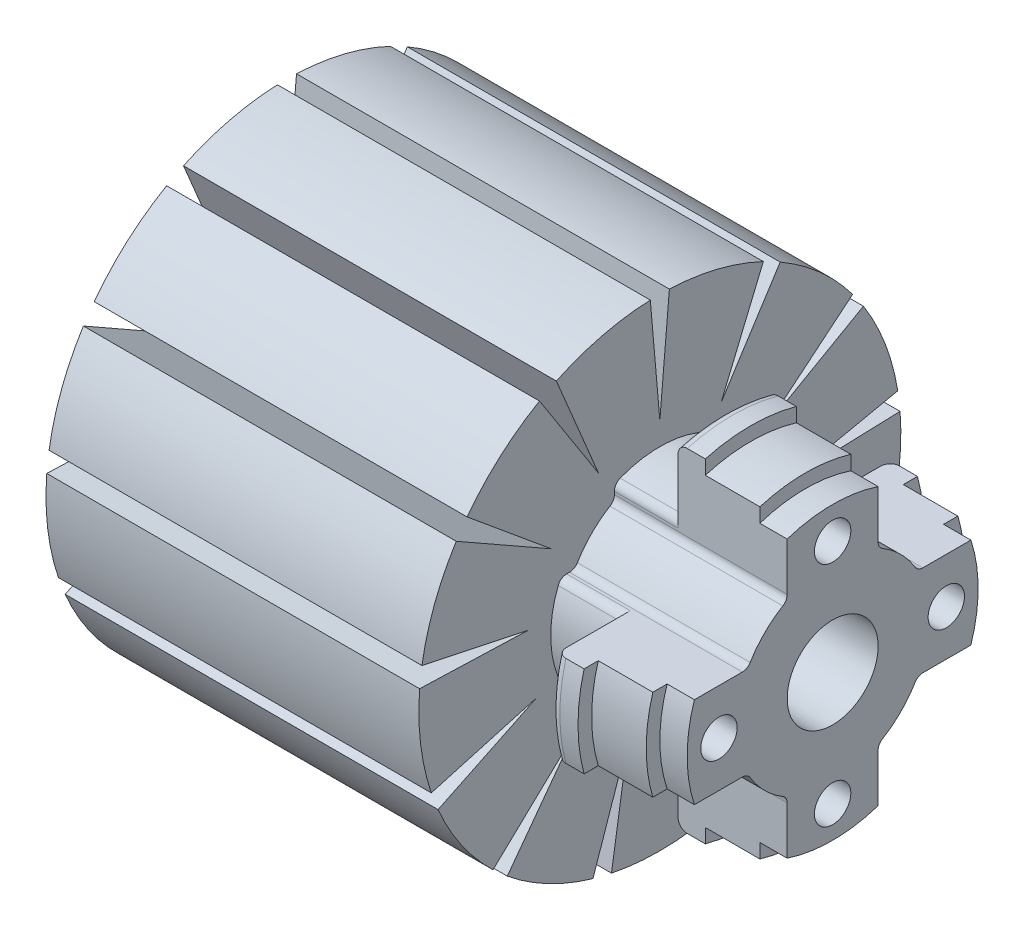
SolidWorks part; units mm, degrees
ref_plane "Front Plane" through (0, 0, 0) normal (0, 0, 1) x (1, 0, 0)
ref_plane "Top Plane" through (0, 0, 0) normal (0, 1, 0) x (1, 0, 0)
ref_plane "Right Plane" through (0, 0, 0) normal (1, 0, 0) x (0, 0, -1)
sketch "Sketch1" plane through (0, 0, 0) normal (1, 0, 0) x (0, 0, -1)
  circle A0 centre (0, 0) radius 26.5
  circle A1 centre (0, 0) radius 5
  dimension "D1" = 53
  dimension "D2" = 10
extrude "Extrude1" add sketch "Sketch1" along normal blind 60
sketch "Sketch2" plane through (0, 0, 0) normal (0, 0, 1) x (1, 0, 0)
  line L0 (0, 0) -> (31, 0) construction
  line L1 (0, 26.5) -> (0, -26.5) construction
  line L3 (60, 26.5) -> (41, 26.5)
  line L4 (60, 26.5) -> (60, 0)
  line L6 (41, 26.5) -> (41, 12)
  line L8 (60, 0) -> (60, 16)
  line L9 (60, 16) -> (57, 16)
  line L12 (57, 16) -> (57, 17.5)
  line L13 (57, 17.5) -> (51, 17.5)
  line L16 (51, 17.5) -> (51, 19)
  line L17 (51, 19) -> (48, 19)
  line L18 (48, 12) -> (48, 19)
  line L21 (48, 12) -> (41, 12)
  dimension "D1" = 12
  dimension "D2" = 7.5
  dimension "D3" = 9
  dimension "D4" = 10.5
  dimension "D5" = 7
  dimension "D6" = 3
  dimension "D7" = 6
  dimension "D8" = 19
revolve "Cut-Revolve1" cut sketch "Sketch2" angle 360 about L0
sketch "Sketch3" plane through (60, 0, 0) normal (1, 0, 0) x (0, 0, -1)
  circle A0 centre (0, 12.5) radius 2
  circle A1 centre (12.5, 0) radius 2
  circle A2 centre (0, -12.5) radius 2
  circle A3 centre (-12.5, 0) radius 2
  dimension "D1" = 4
  dimension "D2" = 12.5
extrude "Extrude2" cut sketch "Sketch3" against normal blind 10
sketch "Sketch4" plane through (0, 0, 0) normal (-1, 0, 0) x (0, 0, 1)
  line L1 (1.0481, 26.4793) -> (0, 14.5)
  line L2 (-1.0481, 26.4793) -> (0, 14.5)
  line L4 (13.2335, 22.9592) -> (6.7385, 12.8391)
  line L5 (11.3775, 23.9333) -> (6.7385, 12.8391)
  line L7 (22.3874, 14.1794) -> (11.9333, 8.2369)
  line L8 (21.1966, 15.9045) -> (11.9333, 8.2369)
  line L10 (26.4125, 2.1513) -> (14.3943, 1.7478)
  line L11 (26.1599, 4.2321) -> (14.3943, 1.7478)
  line L13 (24.3869, -10.3696) -> (13.5577, -5.1418)
  line L14 (25.1302, -8.4097) -> (13.5577, -5.1418)
  line L16 (16.7745, -20.515) -> (9.6153, -10.8534)
  line L17 (18.3435, -19.125) -> (9.6153, -10.8534)
  line L19 (5.3193, -25.9606) -> (3.4701, -14.0787)
  line L20 (7.3545, -25.459) -> (3.4701, -14.0787)
  line L22 (-7.3545, -25.459) -> (-3.4701, -14.0787)
  line L23 (-5.3193, -25.9606) -> (-3.4701, -14.0787)
  line L25 (-18.3435, -19.125) -> (-9.6153, -10.8534)
  line L26 (-16.7745, -20.515) -> (-9.6153, -10.8534)
  line L28 (-25.1302, -8.4097) -> (-13.5577, -5.1418)
  line L29 (-24.3869, -10.3696) -> (-13.5577, -5.1418)
  line L31 (-26.1599, 4.2321) -> (-14.3943, 1.7478)
  line L32 (-26.4125, 2.1513) -> (-14.3943, 1.7478)
  line L34 (-21.1966, 15.9045) -> (-11.9333, 8.2369)
  line L35 (-22.3874, 14.1794) -> (-11.9333, 8.2369)
  line L37 (-11.3775, 23.9333) -> (-6.7385, 12.8391)
  line L38 (-13.2335, 22.9592) -> (-6.7385, 12.8391)
  line L39 (-12.3152, 23.4646) -> (-6.7385, 12.8391) [skipped]
  line L40 (-21.8091, 15.0537) -> (-11.9333, 8.2369) [skipped]
  line L41 (-26.3068, 3.1942) -> (-14.3943, 1.7478) [skipped]
  line L42 (-24.7779, -9.397) -> (-13.5577, -5.1418) [skipped]
  line L43 (-17.5728, -19.8355) -> (-9.6153, -10.8534) [skipped]
  line L44 (-6.3419, -25.73) -> (-3.4701, -14.0787) [skipped]
  line L45 (6.3419, -25.73) -> (3.4701, -14.0787) [skipped]
  line L46 (17.5728, -19.8355) -> (9.6153, -10.8534) [skipped]
  line L47 (24.7779, -9.397) -> (13.5577, -5.1418) [skipped]
  line L48 (26.3068, 3.1942) -> (14.3943, 1.7478) [skipped]
  line L49 (21.8091, 15.0537) -> (11.9333, 8.2369) [skipped]
  line L50 (12.3152, 23.4646) -> (6.7385, 12.8391) [skipped]
  line L51 (0, 26.5) -> (0, 14.5) [skipped]
  circle A0 centre (0, 0) radius 26.5 construction
  circle A1 centre (0, 0) radius 26.5
  circle M1 centre (0, 0) radius 26.5
extrude "Extrude3" cut sketch "Sketch4" against normal up to next contours L35 L34 M1 | L38 L37 M1 | L2 L1 M1 | L5 L4 M1 | L8 L7 M1 | L11 L10 M1 | L14 L13 M1 | L17 L16 M1 | L20 L19 M1 | L23 L22 M1 | L26 L25 M1 | L29 L28 M1 | L32 L31 M1
sketch "Sketch5" plane through (60, 0, 0) normal (1, 0, 0) x (0, 0, -1)
  line L0 (-5, 18.3303) -> (-5, 9.3467)
  line L1 (-9.3467, 5) -> (-18.3303, 5)
  line L2 (18.3303, 5) -> (9.3467, 5)
  line L3 (5, 9.3467) -> (5, 18.3303)
  line L4 (5, -18.3303) -> (5, -9.3467)
  line L5 (9.3467, -5) -> (18.3303, -5)
  line L6 (-18.3303, -5) -> (-9.3467, -5)
  line L7 (-5, -9.3467) -> (-5, -18.3303)
  circle A0 centre (0, 0) radius 10.6
  circle A1 centre (0, 0) radius 19 construction
  circle A2 centre (-12.5, 0) radius 2 construction
  circle A3 centre (0, 12.5) radius 2 construction
  circle A4 centre (0, 0) radius 19
  circle M5 centre (0, 0) radius 16
  dimension "D1" = 21.2
  dimension "D2" = 5
  dimension "D3" = 5
extrude "Extrude4" cut sketch "Sketch5" against normal up to surface (19 mm away) contours A0 L0 L1 M5 | L0 A4 L1 M5 | A0 L2 L3 M5 | L2 A4 L3 M5 | A0 L4 L5 M5 | L4 A4 L5 M5 | A0 L6 L7 M5 | L6 A4 L7 M5 up to face at (41, 0, 0)
fillet "Fillet1" radius 1 20 edges at (48, -19, 0) (48, 0, 19) (48, 19, 0) (48, 0, -19) (44.5, 10.9087, -5) (50.5, 9.3467, -5) (50.5, 5, -9.3467) (44.5, 5, -10.9087) (44.5, -5, -10.9087) (50.5, -5, -9.3467) (50.5, -9.3467, -5) (44.5, -10.9087, -5) (44.5, -10.9087, 5) (50.5, -9.3467, 5) (50.5, -5, 9.3467) (44.5, -5, 10.9087) (44.5, 5, 10.9087) (50.5, 5, 9.3467) (44.5, 10.9087, 5) (50.5, 9.3467, 5)
